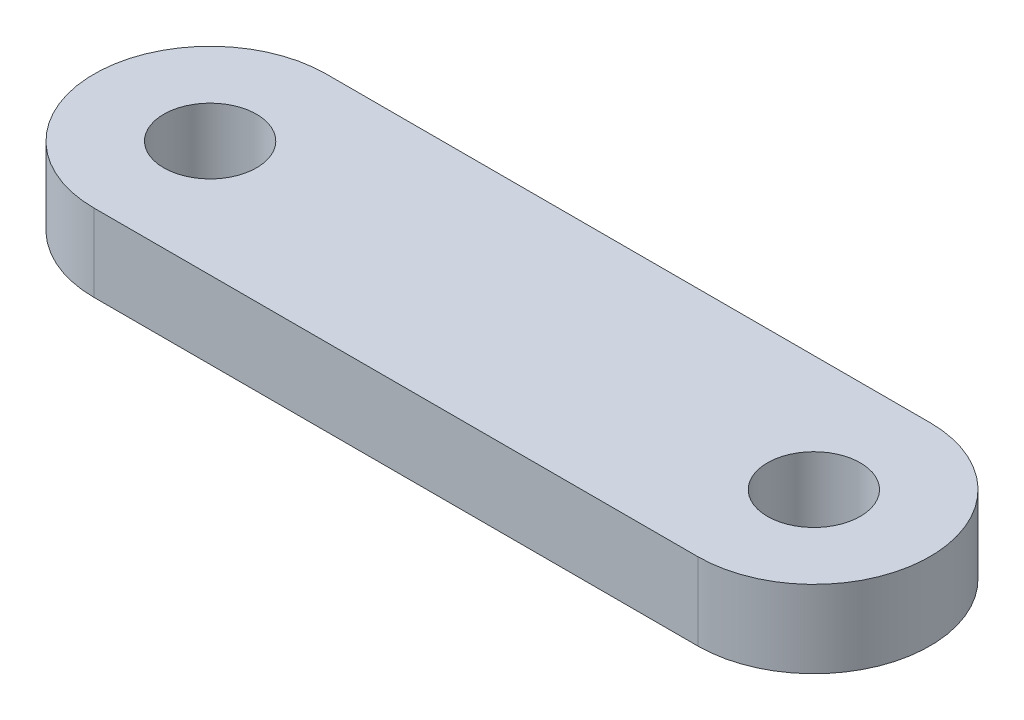
SolidWorks part; units mm, degrees
ref_plane "Front Plane" through (0, 0, 0) normal (0, 0, 1) x (1, 0, 0)
ref_plane "Top Plane" through (0, 0, 0) normal (0, 1, 0) x (1, 0, 0)
ref_plane "Right Plane" through (0, 0, 0) normal (1, 0, 0) x (0, 0, -1)
sketch "Sketch1" plane through (0, 0, 0) normal (0, 1, 0) x (1, 0, 0)
  line L0 (0, 7.5) -> (39, 7.5)
  line L1 (0, -7.5) -> (39, -7.5)
  arc A0 (0, 7.5) -> (0, -7.5) centre (0, 0) ccw
  arc A1 (39, -7.5) -> (39, 7.5) centre (39, 0) ccw
  circle A2 centre (39, 0) radius 3
  circle A3 centre (0, 0) radius 3
  dimension "D1" = 15
  dimension "D2" = 39
  dimension "D3" = 6
  dimension "D4" = 6
extrude "Boss-Extrude1" add sketch "Sketch1" along normal blind 5
